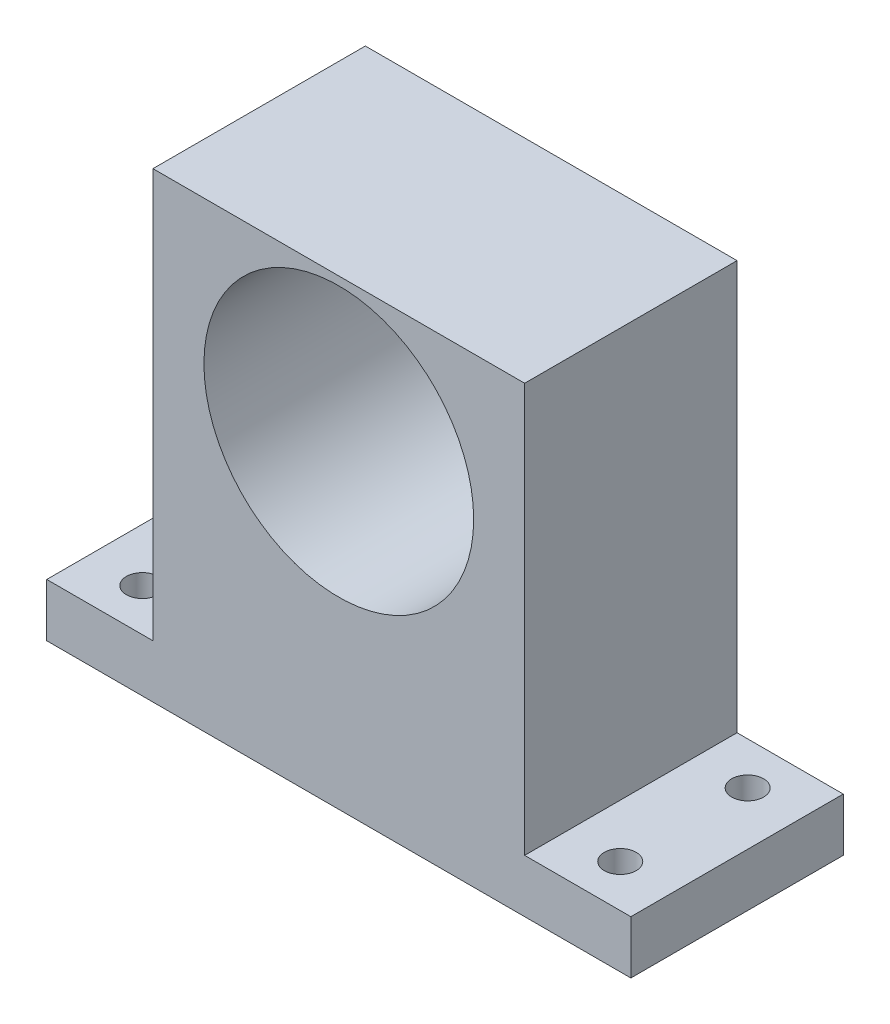
SolidWorks part; units mm, degrees
ref_plane "Спереди" through (0, 0, 0) normal (0, 0, 1) x (1, 0, 0)
ref_plane "Сверху" through (0, 0, 0) normal (0, 1, 0) x (1, 0, 0)
ref_plane "Справа" through (0, 0, 0) normal (1, 0, 0) x (0, 0, -1)
sketch "Эскиз1" plane through (0, 0, 0) normal (0, 0, 1) x (1, 0, 0)
  line L1 (-17.5, -21.75) -> (17.5, -21.75)
  line L2 (-17.5, -21.75) -> (-17.5, 21.75)
  line L3 (-17.5, 21.75) -> (17.5, 21.75)
  line L4 (17.5, -21.75) -> (17.5, 21.75)
  line L5 (-17.5, -21.75) -> (17.5, 21.75) construction
  line L6 (-17.5, 21.75) -> (17.5, -21.75) construction
  point P0 (0, 0)
  dimension "D1" = 35
  dimension "D2" = 43.5
extrude "Бобышка-Вытянуть1" add sketch "Эскиз1" along normal blind 20
sketch "Эскиз2" plane through (17.5, 0, 0) normal (1, 0, 0) x (0, 0, -1)
  line L0 (0, -21.75) -> (0, 21.75) construction
  line L1 (-20, -21.75) -> (0, -21.75)
  line L2 (-20, -21.75) -> (-20, -16.75)
  line L3 (-20, -16.75) -> (0, -16.75)
  line L4 (0, -21.75) -> (0, -16.75)
  dimension "D1" = 5
extrude "Бобышка-Вытянуть2" add sketch "Эскиз2" along normal blind 10
sketch "Эскиз3" plane through (-17.5, 0, 0) normal (-1, 0, 0) x (0, 0, 1)
  line L0 (20, 21.75) -> (20, -21.75) construction
  line L1 (0, -21.75) -> (20, -21.75)
  line L2 (0, -21.75) -> (0, -16.75)
  line L3 (0, -16.75) -> (20, -16.75)
  line L4 (20, -21.75) -> (20, -16.75)
  dimension "D1" = 5
extrude "Бобышка-Вытянуть3" add sketch "Эскиз3" along normal blind 10
sketch "Эскиз4" plane through (0, -16.75, 0) normal (0, 1, 0) x (1, 0, 0)
  line L0 (27.5, 0) -> (27.5, -20) construction
  line L1 (27.5, -20) -> (17.5, -20) construction
  line L2 (27.5, 0) -> (17.5, 0) construction
  line L3 (-27.5, -20) -> (-17.5, -20) construction
  line L4 (-27.5, -20) -> (-27.5, 0) construction
  line L5 (-27.5, 0) -> (-17.5, 0) construction
  circle A0 centre (-22.5, -16) radius 1.5
  circle A1 centre (-22.5, -4) radius 1.5
  circle A2 centre (22.5, -16) radius 1.5
  circle A3 centre (22.5, -4) radius 1.5
  dimension "D1" = 3
  dimension "D2" = 3
  dimension "D3" = 3
  dimension "D4" = 3
  dimension "D5" = 5
  dimension "D6" = 4
  dimension "D7" = 5
  dimension "D8" = 4
  dimension "D9" = 4
  dimension "D10" = 5
  dimension "D11" = 5
  dimension "D12" = 4
extrude "Вырез-Вытянуть2" cut sketch "Эскиз4" against normal blind 5
sketch "Эскиз5" plane through (0, 0, 0) normal (0, 0, -1) x (-1, 0, 0)
  line L0 (27.5, -21.75) -> (-27.5, -21.75) construction
  line L1 (-17.5, -16.75) -> (-17.5, 21.75) construction
  circle A0 centre (0, 8.25) radius 12.7
  dimension "D1" = 30
  dimension "D2" = 25.4
  dimension "D3" = 17.5
extrude "Вырез-Вытянуть3" cut sketch "Эскиз5" against normal blind 20
